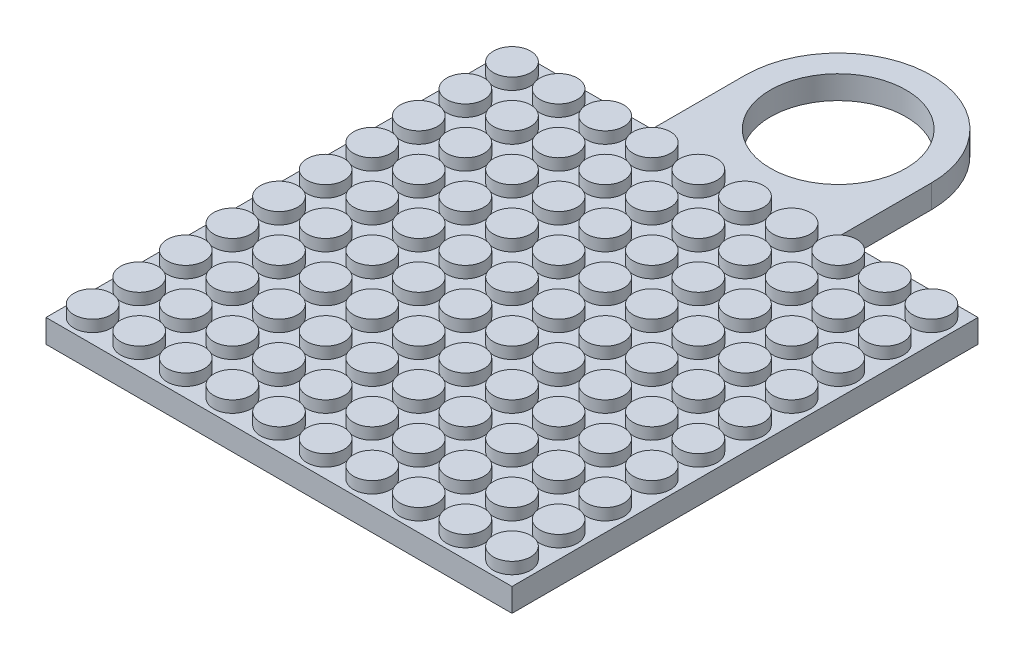
SolidWorks part; units mm, degrees
ref_plane "Front Plane" through (0, 0, 0) normal (0, 0, 1) x (1, 0, 0)
ref_plane "Top Plane" through (0, 0, 0) normal (0, 1, 0) x (1, 0, 0)
ref_plane "Right Plane" through (0, 0, 0) normal (1, 0, 0) x (0, 0, -1)
sketch "Sketch1" plane through (0, 0, 0) normal (0, 1, 0) x (1, 0, 0)
  line L1 (5, -5) -> (-5, -5)
  line L2 (5, -5) -> (5, 5)
  line L3 (5, 5) -> (-5, 5)
  line L4 (-5, -5) -> (-5, 5)
  line L5 (5, -5) -> (-5, 5) construction
  line L6 (5, 5) -> (-5, -5) construction
  point P0 (0, 0)
  dimension "D1" = 10
  dimension "D2" = 10
extrude "Plate" add sketch "Sketch1" along normal blind 0.5
sketch "Sketch2" plane through (0, 0.5, 0) normal (0, 1, 0) x (1, 0, 0)
  line L0 (-5, -5) -> (5, -5) construction
  line L1 (-5, 5) -> (-5, -5) construction
  circle A0 centre (-4.5, -4.5) radius 0.4
  dimension "D1" = 0.8
  dimension "D2" = 0.5
  dimension "D3" = 0.5
extrude "Rod" add sketch "Sketch2" along normal blind 0.25 contours A0
pattern_linear "LPattern1" count 10 spacing 1 along (1, 0, 0) count 10 spacing 1 along (0, 0, -1) of "Rod"
sketch "Sketch4" plane through (0, 0, 0) normal (0, 1, 0) x (1, 0, 0)
  line L5 (-2, 7) -> (-2, 5)
  line L6 (5, 5) -> (-5, 5) construction
  line L8 (-5, 5) -> (-5, -5) construction
  line L9 (-2, 5) -> (2, 5)
  line L10 (2, 5) -> (2, 7)
  arc A0 (-2, 7) -> (2, 7) centre (0, 7) cw
  point P0 (0, 7)
  dimension "D3" = 5
extrude "Boss-Extrude3" add sketch "Sketch4" along normal blind 0.5
sketch "Sketch5" plane through (0, 0.5, 0) normal (0, 1, 0) x (1, 0, 0)
  circle A0 centre (0, 7) radius 1.4559
extrude "Cut-Extrude1" cut sketch "Sketch5" against normal blind 1.5 and the other way blind 0.5
